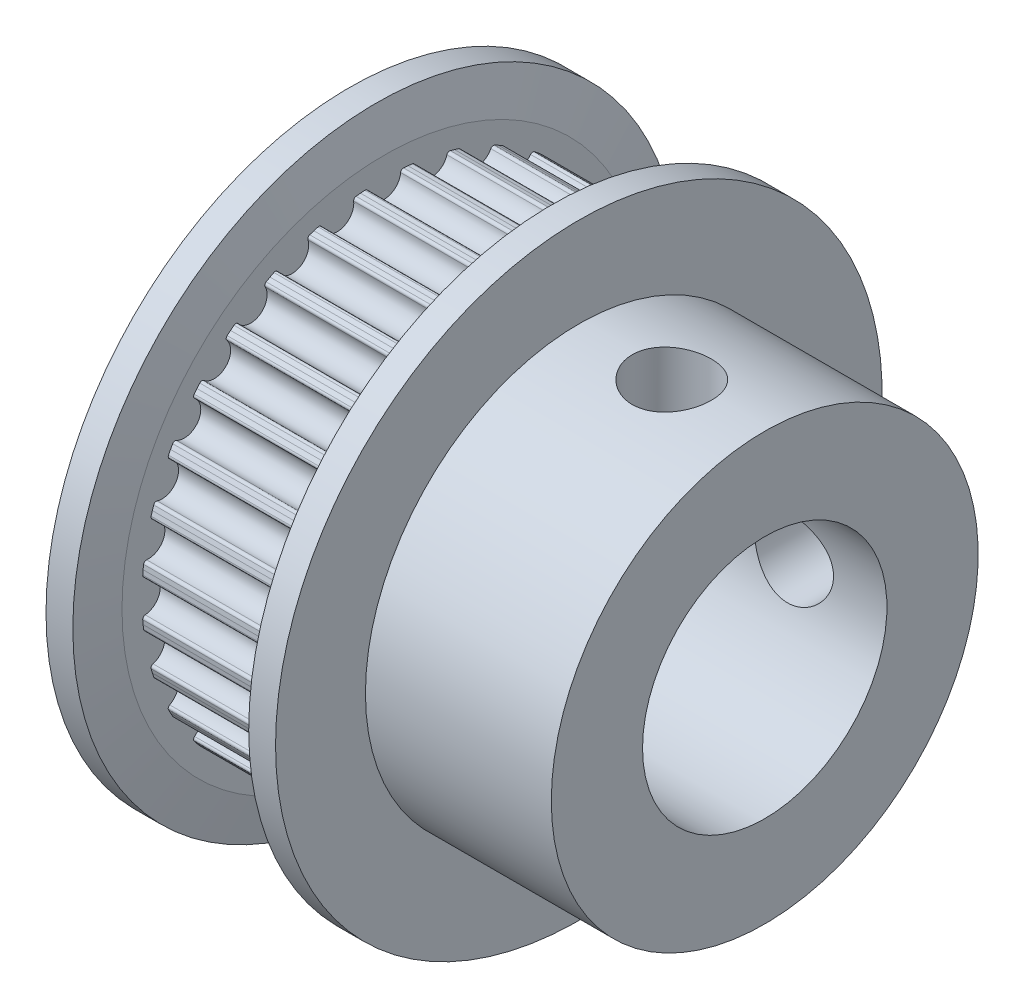
SolidWorks part; units mm, degrees
ref_plane "Front Plane" through (0, 0, 0) normal (0, 0, 1) x (1, 0, 0)
ref_plane "Top Plane" through (0, 0, 0) normal (0, 1, 0) x (1, 0, 0)
ref_plane "Right Plane" through (0, 0, 0) normal (1, 0, 0) x (0, 0, -1)
ref_plane "Plane1" through (0, 0, 0) normal (0, 0, 1) x (1, 0, 0)
sketch "Sketch1" plane through (0, 0, 0) normal (0, 0, 1) x (1, 0, 0)
  line L0 (0, 0) -> (0, 8.75)
  line L1 (0, 8.75) -> (1.43, 8.75)
  line L2 (1.43, 8.75) -> (1.43, 10.0881)
  line L3 (1.43, 10.0881) -> (7.98, 10.0881)
  line L4 (7.98, 10.0881) -> (7.98, 8.75)
  line L5 (7.98, 8.75) -> (17.03, 8.75)
  line L6 (17.03, 8.75) -> (17.03, 0)
  line L7 (17.03, 0) -> (0, 0)
  line L8 (17.03, 0) -> (0, 0) construction
  dimension "D1" = 6.55
  dimension "D2" = 8.75
  dimension "D3" = 1.43
  dimension "D4" = 9.05
  dimension "D5" = 10.0881
revolve "Revolve1" add sketch "Sketch1" angle 360 about L8
sketch "Sketch2" plane through (1.43, 0, 0) normal (1, 0, 0) x (0, 0, -1)
  line L0 (-1.0344, 9.88) -> (-1.0578, 10.1299)
  line L1 (-0.793, 9.8993) -> (-1.0344, 9.88)
  line L2 (0.793, 9.8993) -> (1.0344, 9.88)
  line L3 (1.0344, 9.88) -> (1.0578, 10.1299)
  line L4 (0, 10.185) -> (0, 0) construction
  arc A0 (-0.6724, 9.7974) -> (-0.793, 9.8993) centre (-0.784, 9.7876) ccw
  arc A1 (-0.6724, 9.7974) -> (0.6724, 9.7974) centre (0, 9.856) ccw
  arc A2 (0.6724, 9.7974) -> (0.793, 9.8993) centre (0.784, 9.7876) cw
  arc A3 (1.0578, 10.1299) -> (-1.0578, 10.1299) centre (0, 0) ccw
  dimension "D2" = 0.675
  dimension "D1" = 9.856
  dimension "D3" = 9.931
extrude "Cut-Extrude1" cut sketch "Sketch2" against normal up to surface
ref_axis "Axis1" through (17.03, 0, 0) along (-1, 0, 0)
pattern_circular "CirPattern1" count 32 over 360 about axis through (0, 0, 0) along (1, 0, 0) of "Cut-Extrude1"
sketch "Sketch34" plane through (0, 0, 0) normal (0, 0, 1) x (1, 0, 0)
  line L0 (7.98, 8.75) -> (7.98, 10.75)
  line L1 (7.98, 10.75) -> (8.31, 12.435)
  line L2 (8.31, 12.435) -> (9.41, 12.435)
  line L3 (9.41, 12.435) -> (9.41, 8.75)
  line L4 (17.03, 8.75) -> (7.98, 8.75) construction
  line L5 (9.41, 8.75) -> (7.98, 8.75)
  line L6 (17.03, 0) -> (7.98, 0) construction
  line L7 (1.43, 8.75) -> (1.43, 10.75)
  line L8 (1.43, 10.75) -> (1.1, 12.435)
  line L9 (1.1, 12.435) -> (0, 12.435)
  line L10 (0, 12.435) -> (0, 8.76)
  line L11 (0.01, 8.75) -> (1.43, 8.75)
  line L12 (0, 8.76) -> (0.01, 8.75)
  point P16 (0, 8.75)
  dimension "D1" = 1.43
  dimension "D2" = 12.435
  dimension "D3" = 1.1
  dimension "D4" = 10.75
revolve "Revolve2" add sketch "Sketch34" angle 360 about L6
sketch "Sketch39" plane through (0, 0, 0) normal (-1, 0, 0) x (0, 0, 1)
  circle A0 centre (0, 0) radius 5.01
  dimension "D1" = 10.02
extrude "Cut-Extrude2" cut sketch "Sketch39" against normal up to surface (17.03 mm away) up to face at (17.03, 0, 8.75)
ref_plane "Plane39" through (13.22, 0, 0) normal (1, 0, 0) x (0, 0, -1)
sketch "Sketch37" plane through (13.22, 0, 0) normal (1, 0, 0) x (0, 0, -1)
  line L0 (0, 9.93) -> (1.621, 9.93)
  line L1 (1.621, 9.93) -> (1.621, 0)
  line L2 (1.621, 0) -> (0, 0)
  line L3 (0, 0) -> (0, 9.93)
  line L4 (0, 0) -> (0, 9.93) construction
revolve "Cut-Revolve2" cut sketch "Sketch37" angle 360 about L4
pattern_circular "CirPattern2" count 2 over 90 about axis through (17.03, 0, 0) along (-1, 0, 0) of "Cut-Revolve2"
ref_plane "Plane40" through (4.705, 0, 0) normal (-1, 0, 0) x (0, 0, 1)
